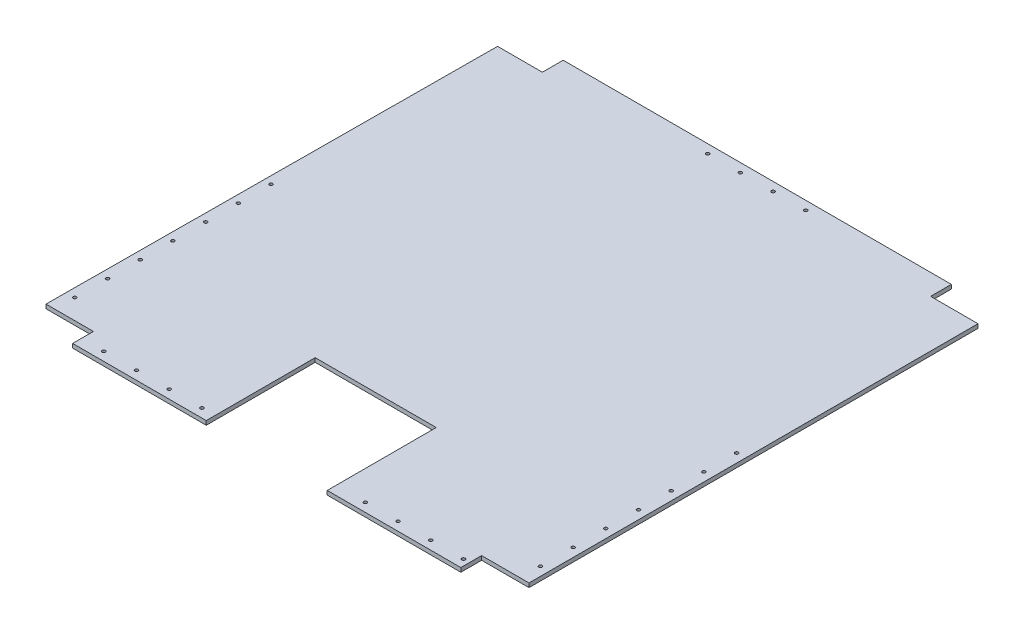
SolidWorks part; units mm, degrees
ref_plane "Front Plane" through (0, 0, 0) normal (0, 0, 1) x (1, 0, 0)
ref_plane "Top Plane" through (0, 0, 0) normal (0, 1, 0) x (1, 0, 0)
ref_plane "Right Plane" through (0, 0, 0) normal (1, 0, 0) x (0, 0, -1)
sketch "Sketch1" plane through (0, 329.9257, 0) normal (0, 1, 0) x (1, 0, 0)
  line L0 (507.7249, 70.7173) -> (507.7249, 45.3173)
  line L2 (507.7249, 45.3173) -> (565.6999, 45.3173)
  line L3 (32.8749, 45.3173) -> (-21.9251, 45.3173) construction
  line L4 (-21.9251, 45.3173) -> (32.8749, 45.3173)
  line L5 (32.8749, 70.7173) -> (507.7249, 70.7173)
  line L6 (32.8749, 45.3173) -> (32.8749, 70.7173)
  line L9 (565.6999, 45.3173) -> (565.6999, -503.8827)
  line L10 (565.6999, -503.8827) -> (570.6999, -503.8827) construction
  line L12 (540.2999, -529.2827) -> (0.2999, -529.2827) construction
  line L13 (510.6999, -529.2827) -> (29.8999, -529.2827) construction
  line L14 (344.2999, -396.0177) -> (196.2999, -396.0177)
  line L15 (196.2999, -396.0177) -> (196.2999, -529.2827)
  line L16 (196.2999, -529.2827) -> (32.8749, -529.2827)
  line L17 (32.8749, -529.2827) -> (32.8749, -503.8827)
  line L18 (32.8749, -503.8827) -> (-25.1001, -503.8827)
  line L19 (-25.1001, -503.8827) -> (-21.9251, 45.3173)
  line L20 (344.2999, -529.2827) -> (344.2999, -396.0177)
  line L21 (340.2999, -465.0177) -> (344.2999, -465.0177) construction
  line L22 (340.2999, -530.0177) -> (340.2999, -400.0177) construction
  line L23 (200.2999, -465.0177) -> (196.2999, -465.0177) construction
  line L24 (200.2999, -400.0177) -> (200.2999, -530.0177) construction
  line L25 (270.2999, -396.0177) -> (270.2999, -400.0177) construction
  line L26 (340.2999, -400.0177) -> (200.2999, -400.0177) construction
  line L27 (565.6999, -529.2827) -> (565.6999, 70.7173) construction
  line L28 (344.2999, -529.2827) -> (507.7249, -529.2827)
  line L29 (507.7249, -529.2827) -> (507.7249, -503.8827)
  line L30 (540.2999, -503.8827) -> (0.2999, -503.8827) construction
  line L31 (507.7249, -503.8827) -> (565.6999, -503.8827)
  line L40 (-21.9251, -223.9327) -> (-21.9251, -207.7827) construction
  line L41 (510.6999, 70.7173) -> (29.8999, 70.7173) construction
  point P16 (35.061, 70.7173)
  dimension "D1" = 4
extrude "Boss-Extrude1" add sketch "Sketch1" along normal blind 5
sketch "Sketch2" plane through (0, 329.9257, 0) normal (0, -1, 0) x (1, 0, 0)
  circle A0 centre (60.2999, 518.6077) radius 2
  circle A1 centre (380.2999, 518.6077) radius 2
  circle A2 centre (220.2999, -60.0423) radius 2
  circle A3 centre (100.2999, 518.6077) radius 2
  circle A4 centre (420.2999, 518.6077) radius 2
  circle A5 centre (260.2999, -60.0423) radius 2
  circle A6 centre (140.2999, 518.6077) radius 2
  circle A7 centre (460.2999, 518.6077) radius 2
  circle A8 centre (300.2999, -60.0423) radius 2
  circle A9 centre (180.2999, 518.6077) radius 2
  circle A10 centre (500.2999, 518.6077) radius 2
  circle A11 centre (340.2999, -60.0423) radius 2
  circle A12 centre (-14.4251, 239.2827) radius 2
  circle A13 centre (555.0249, 239.2827) radius 2
  circle A14 centre (-14.4251, 279.2827) radius 2
  circle A15 centre (555.0249, 279.2827) radius 2
  circle A16 centre (-14.4251, 319.2827) radius 2
  circle A17 centre (555.0249, 319.2827) radius 2
  circle A18 centre (-14.4251, 359.2827) radius 2
  circle A19 centre (555.0249, 359.2827) radius 2
  circle A20 centre (-14.4251, 399.2827) radius 2
  circle A21 centre (555.0249, 399.2827) radius 2
  circle A22 centre (-14.4251, 439.2827) radius 2
  circle A23 centre (555.0249, 439.2827) radius 2
  circle A24 centre (-14.4251, 479.2827) radius 2
  circle A25 centre (555.0249, 479.2827) radius 2
  dimension "D1" = 4
  dimension "D3" = 40
  dimension "D4" = 4
  dimension "D6" = 40
  dimension "D2" = 4
  dimension "D5" = 7
extrude "Cut-Extrude1" cut sketch "Sketch2" against normal through all
